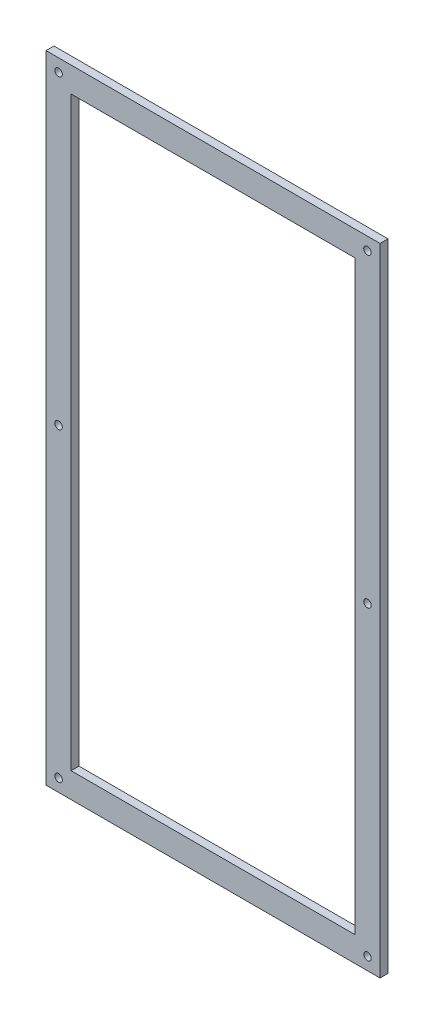
SolidWorks part; units mm, degrees
ref_plane "Front Plane" through (0, 0, 0) normal (0, 0, 1) x (1, 0, 0)
ref_plane "Top Plane" through (0, 0, 0) normal (0, 1, 0) x (1, 0, 0)
ref_plane "Right Plane" through (0, 0, 0) normal (1, 0, 0) x (0, 0, -1)
sketch "Sketch1" plane through (0, 0, 0) normal (0, 0, 1) x (1, 0, 0)
  line L0 (0, 0) -> (0, 254)
  line L1 (0, 254) -> (133.35, 254)
  line L2 (133.35, 254) -> (133.35, 0)
  line L3 (133.35, 0) -> (0, 0)
  line L4 (10, 10) -> (10, 244)
  line L5 (10, 244) -> (123.35, 244)
  line L6 (123.35, 244) -> (123.35, 10)
  line L7 (123.35, 10) -> (10, 10)
  line L8 (66.675, 254) -> (66.675, 0) construction
  line L9 (0, 127) -> (133.35, 127) construction
  circle A0 centre (5, 5) radius 1.5
  circle A1 centre (5, 249) radius 1.5
  circle A4 centre (5, 127) radius 1.5
  circle A5 centre (128.35, 249) radius 1.5
  circle A6 centre (128.35, 127) radius 1.5
  circle A7 centre (128.35, 5) radius 1.5
  dimension "D7" = 3
  dimension "D10" = 3
  dimension "D1" = 254
  dimension "D2" = 133.35
  dimension "D3" = 10
  dimension "D4" = 10
  dimension "D5" = 10
  dimension "D6" = 10
  dimension "D8" = 5
  dimension "D9" = 5
extrude "Boss-Extrude1" add sketch "Sketch1" along normal blind 3.175
